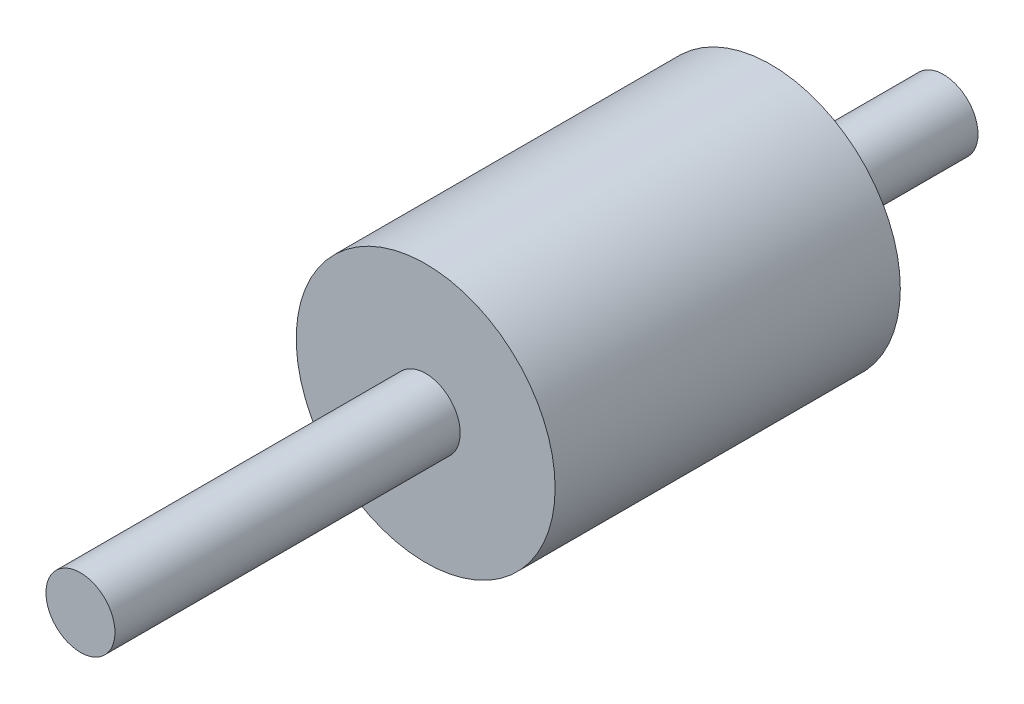
SolidWorks part; units mm, degrees
ref_plane "Front Plane" through (0, 0, 0) normal (0, 0, 1) x (1, 0, 0)
ref_plane "Top Plane" through (0, 0, 0) normal (0, 1, 0) x (1, 0, 0)
ref_plane "Right Plane" through (0, 0, 0) normal (1, 0, 0) x (0, 0, -1)
sketch "Sketch1" plane through (0, 0, 0) normal (0, 0, 1) x (1, 0, 0)
  circle A0 centre (0, 0) radius 7.5
extrude "Boss-Extrude1" add sketch "Sketch1" along normal blind 20
sketch "Sketch2" plane through (0, 0, 0) normal (0, 0, 1) x (1, 0, 0)
  circle A0 centre (0, 0) radius 1
extrude "Boss-Extrude3" add sketch "Sketch2" along normal blind 40 and the other way blind 10
sketch "Sketch3" plane through (0, 0, 0) normal (0, 0, 1) x (1, 0, 0)
  circle A1 centre (0, 0) radius 2
  dimension "D1" = 4
extrude "Boss-Extrude4" add sketch "Sketch3" against normal blind 10 and the other way blind 40
